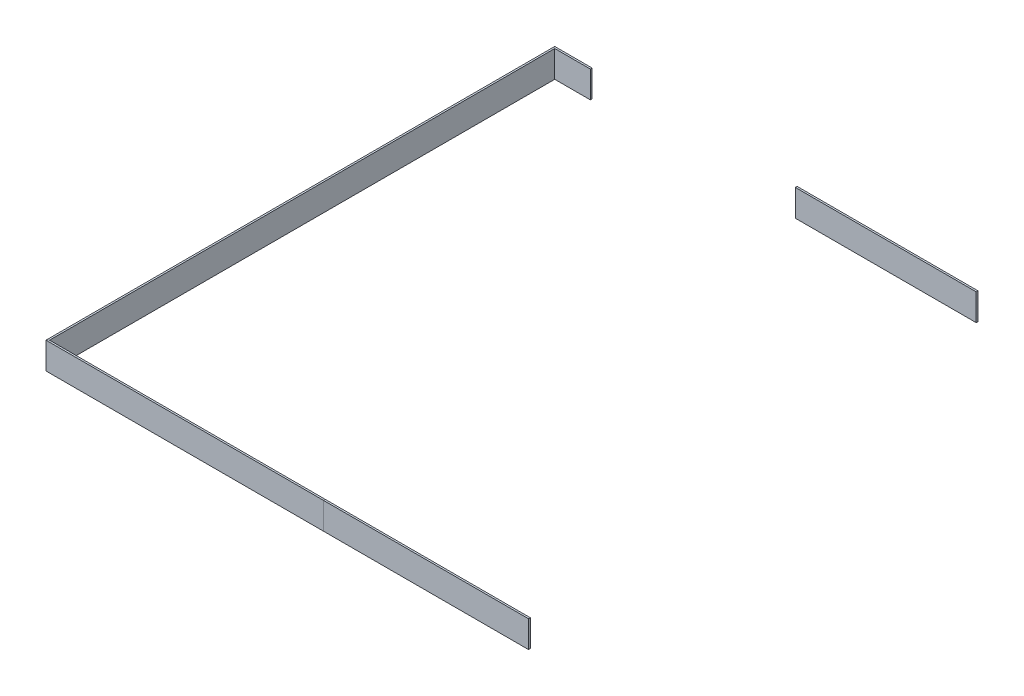
SolidWorks part; units mm, degrees
ref_plane "Front" through (0, 0, 0) normal (0, 0, 1) x (1, 0, 0)
ref_plane "Top" through (0, 0, 0) normal (0, 1, 0) x (1, 0, 0)
ref_plane "Right" through (0, 0, 0) normal (1, 0, 0) x (0, 0, -1)
sketch "Sketch2" plane through (0, 0, 0) normal (1, 0, 0) x (0, 0, -1)
  line L0 (0, 0) -> (0, 19.05)
  line L1 (0, 19.05) -> (1.27, 19.05)
  line L2 (1.27, 0) -> (1.27, 19.05)
  line L5 (1.27, 0) -> (0, 0)
  dimension "D3" = 1.27
  dimension "D4" = 19.05
sketch "Sketch3" plane through (0, 0, 0) normal (0, 1, 0) x (1, 0, 0)
  line L0 (0, 0) -> (-342.9, 0)
  line L1 (-342.9, 0) -> (-342.9, -360.3625)
  line L2 (-342.9, -360.3625) -> (-146.05, -360.3625)
  line L4 (-146.05, -360.3625) -> (0, -360.3625)
  dimension "D1" = 342.9
  dimension "D2" = 360.3625
sweep "L-Bracket" add profiles "Sketch2" path "Sketch3"
sketch "Sketch4" plane through (0, 0, -1.27) normal (0, 0, -1) x (-1, 0, 0)
  line L1 (0, 27.4511) -> (42.2402, 27.4511)
  line L2 (0, 27.4511) -> (0, -3.132)
  line L3 (0, -3.132) -> (42.2402, -3.132)
  line L4 (42.2402, 27.4511) -> (42.2402, -3.132)
  line L5 (0, 0) -> (0, 19.05) construction
  line L7 (171.323, 30.4983) -> (317.5, 30.4983)
  line L8 (171.323, 30.4983) -> (171.323, -6.7832)
  line L9 (171.323, -6.7832) -> (317.5, -6.7832)
  line L10 (317.5, 30.4983) -> (317.5, -6.7832)
  dimension "D1" = 42.2402
  dimension "D2" = 171.323
  dimension "D3" = 146.177
extrude "Notches" cut sketch "Sketch4" against normal blind 5.08
